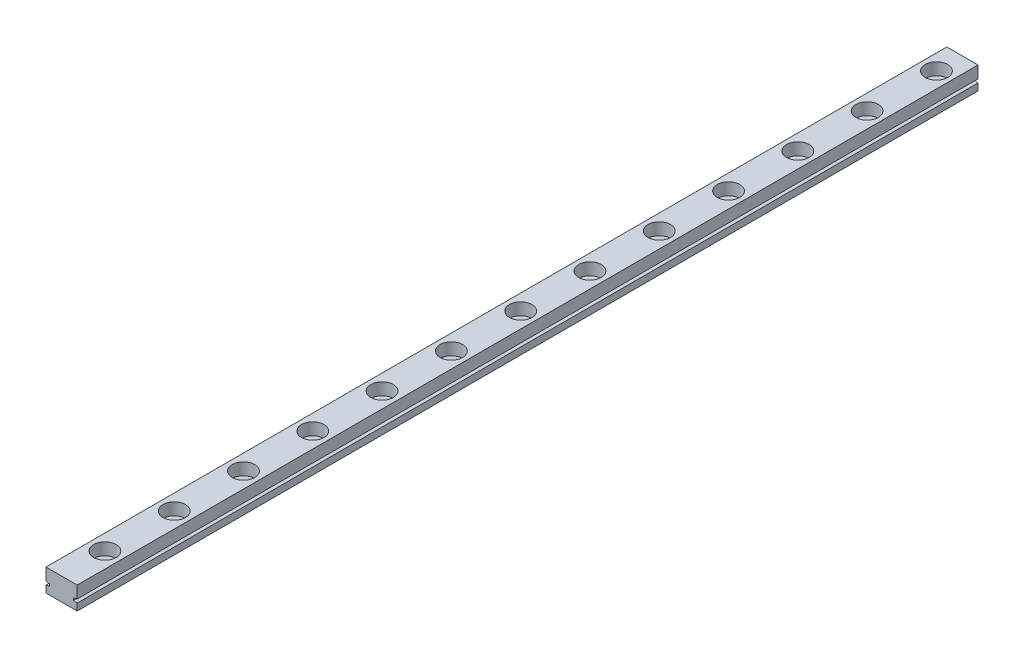
SolidWorks part; units mm, degrees
material "不锈钢 (铁素体)"
ref_plane "前视基准面" through (0, 0, 0) normal (0, 0, 1) x (1, 0, 0)
ref_plane "上视基准面" through (0, 0, 0) normal (0, 1, 0) x (1, 0, 0)
ref_plane "右视基准面" through (0, 0, 0) normal (1, 0, 0) x (0, 0, -1)
sketch "草图1" plane through (0, 0, 0) normal (0, 0, 1) x (1, 0, 0)
  line L1 (-4.5, 3.25) -> (4.5, 3.25)
  line L2 (-4.5, 3.25) -> (-4.5, -3.25)
  line L3 (-4.5, -3.25) -> (4.5, -3.25)
  line L4 (4.5, 3.25) -> (4.5, -3.25)
  line L5 (-4.5, 3.25) -> (4.5, -3.25) construction
  line L6 (-4.5, -3.25) -> (4.5, 3.25) construction
  point P0 (0, 0)
  dimension "D1" = 6.5
  dimension "D2" = 9
extrude "凸台-拉伸1" add sketch "草图1" along normal blind 260
sketch "草图2" plane through (0, 3.25, 0) normal (0, 1, 0) x (1, 0, 0)
  line L0 (0, 0) -> (0, -84.8716) construction
  line L1 (4.5, 0) -> (-4.5, 0) construction
  circle A0 centre (0, -7.5) radius 1.75
  circle A1 centre (0, -27.5) radius 1.75
  circle A2 centre (0, -47.5) radius 1.75
  circle A3 centre (0, -67.5) radius 1.75
  circle A4 centre (0, -87.5) radius 1.75
  circle A5 centre (0, -107.5) radius 1.75
  circle A6 centre (0, -127.5) radius 1.75
  circle A7 centre (0, -147.5) radius 1.75
  circle A8 centre (0, -167.5) radius 1.75
  circle A9 centre (0, -187.5) radius 1.75
  circle A10 centre (0, -207.5) radius 1.75
  circle A11 centre (0, -227.5) radius 1.75
  circle A12 centre (0, -247.5) radius 1.75
  circle A13 centre (0, -267.5) radius 1.75
  circle A14 centre (0, -287.5) radius 1.75
  circle A15 centre (0, -307.5) radius 1.75
  circle A16 centre (0, -327.5) radius 1.75
  circle A17 centre (0, -347.5) radius 1.75
  circle A18 centre (0, -367.5) radius 1.75
  circle A19 centre (0, -387.5) radius 1.75
  dimension "D1" = 3.5
  dimension "D2" = 7.5
  dimension "D4" = 20
  dimension "D3" = 20
extrude "切除-拉伸1" cut sketch "草图2" against normal through all
sketch "草图3" plane through (0, 3.25, 0) normal (0, 1, 0) x (1, 0, 0)
  circle A0 centre (0, -7.5) radius 3.25
  circle A1 centre (0, -27.5) radius 3.25
  circle A2 centre (0, -47.5) radius 3.25
  circle A3 centre (0, -67.5) radius 3.25
  circle A4 centre (0, -87.5) radius 3.25
  circle A5 centre (0, -107.5) radius 3.25
  circle A6 centre (0, -127.5) radius 3.25
  circle A7 centre (0, -147.5) radius 3.25
  circle A8 centre (0, -167.5) radius 3.25
  circle A9 centre (0, -187.5) radius 3.25
  circle A10 centre (0, -207.5) radius 3.25
  circle A11 centre (0, -227.5) radius 3.25
  circle A12 centre (0, -247.5) radius 3.25
  circle A13 centre (0, -267.5) radius 3.25
  circle A14 centre (0, -287.5) radius 3.25
  circle A15 centre (0, -307.5) radius 3.25
  circle A16 centre (0, -327.5) radius 3.25
  circle A17 centre (0, -347.5) radius 3.25
  circle A18 centre (0, -367.5) radius 3.25
  circle A19 centre (0, -387.5) radius 3.25
  dimension "D1" = 6.5
  dimension "D3" = 20
  dimension "D2" = 20
extrude "切除-拉伸2" cut sketch "草图3" against normal blind 3.5
sketch "草图4" plane through (0, 0, 0) normal (0, 0, -1) x (-1, 0, 0)
  line L0 (0, 3.25) -> (0, -3.25) construction
  line L1 (-4.5, 3.25) -> (4.5, 3.25) construction
  line L2 (4.5, -3.25) -> (-4.5, -3.25) construction
  line L3 (4.5, -0.25) -> (3.5, -0.45)
  line L4 (4.5, 3.25) -> (4.5, -3.25) construction
  line L5 (3.5, -0.45) -> (3.5, -1.05)
  line L6 (3.5, -1.05) -> (4.5, -1.25)
  line L7 (3.5, -0.75) -> (8.1318, -0.75) construction
  line L8 (4.5, -0.25) -> (4.5, -1.25)
  line L9 (-4.5, -0.25) -> (-3.5, -0.45)
  line L10 (-3.5, -0.45) -> (-3.5, -1.05)
  line L11 (-3.5, -1.05) -> (-4.5, -1.25)
  line L12 (-4.5, -0.25) -> (-4.5, -1.25)
  dimension "D1" = 1
  dimension "D2" = 1
  dimension "D3" = 0.6
  dimension "D4" = 4
extrude "切除-拉伸3" cut sketch "草图4" against normal through all
